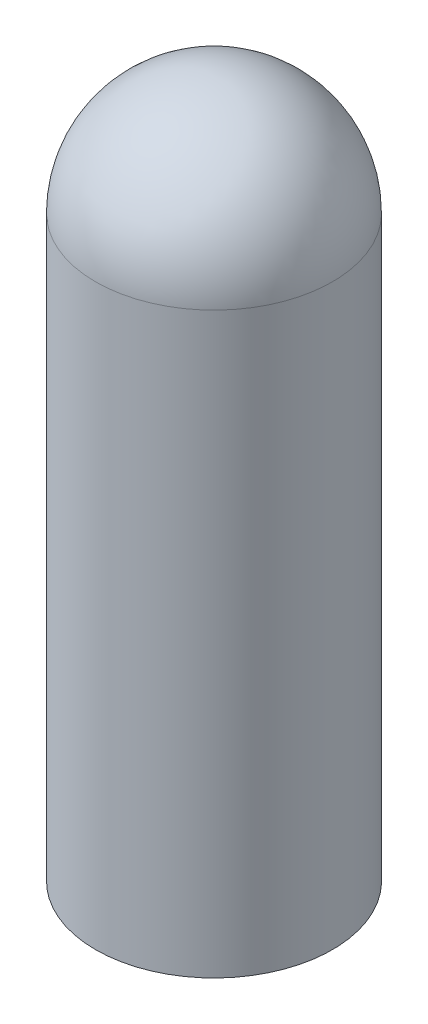
SolidWorks part; units mm, degrees
ref_plane "Front Plane" through (0, 0, 0) normal (0, 0, 1) x (1, 0, 0)
ref_plane "Top Plane" through (0, 0, 0) normal (0, 1, 0) x (1, 0, 0)
ref_plane "Right Plane" through (0, 0, 0) normal (1, 0, 0) x (0, 0, -1)
sketch "Sketch2" plane through (0, 0, 0) normal (0, 1, 0) x (1, 0, 0)
  circle A0 centre (0, 0) radius 21.59
  dimension "D1" = 43.18
extrude "Boss-Extrude1" add sketch "Sketch2" along normal blind 144.78
sketch "Sketch3" plane through (0, 0, 0) normal (0, -1, 0) x (1, 0, 0)
  circle A0 centre (0, 0) radius 19.05
  dimension "D1" = 38.1
extrude "Cut-Extrude1" cut sketch "Sketch3" against normal blind 139.7
fillet "Fillet1" radius 21.59 1 edges at (0, 144.78, 21.59)
fillet "Fillet2" radius 19.05 1 edges at (0, 139.7, -19.05)
sketch "Sketch4" plane through (0, 0, 0) normal (0, -1, 0) x (1, 0, 0)
  circle A0 centre (0, 0) radius 21.59
extrude "Cut-Extrude2" cut sketch "Sketch4" against normal blind 17.78
